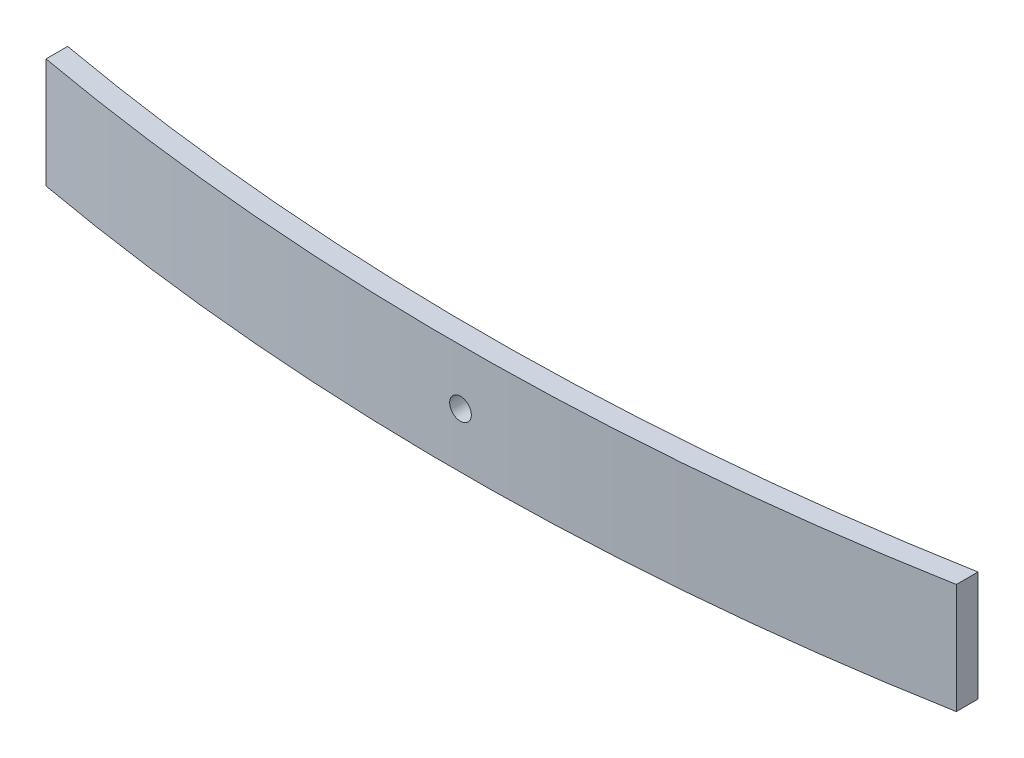
SolidWorks part; units mm, degrees
ref_plane "Front Plane" through (0, 0, 0) normal (0, 0, 1) x (1, 0, 0)
ref_plane "Top Plane" through (0, 0, 0) normal (0, 1, 0) x (1, 0, 0)
ref_plane "Right Plane" through (0, 0, 0) normal (1, 0, 0) x (0, 0, -1)
sketch "Sketch1" plane through (0, 0, 0) normal (0, 1, 0) x (1, 0, 0)
  line L0 (-630, 0) -> (630, 0) construction
  line L1 (-210.8013, -133) -> (245.5549, -133) construction
  line L2 (0, 0) -> (0, -133) construction
  line L3 (-602.5798, 17.4465) -> (-589.9243, 25.4988)
  line L4 (-616.835, -11.5296) -> (-605.5506, -21.4121)
  line L5 (616.835, -11.5296) -> (605.5506, -21.4121)
  line L6 (-630.0217, -47.5) -> (-630.0217, -62.5)
  line L7 (602.5798, 17.4465) -> (589.9243, 25.4988)
  line L8 (630.0217, -47.5) -> (630.0217, -62.5)
  line L9 (-545.0217, -92.3065) -> (-545.0217, -107.3065)
  line L10 (545.0217, -92.3065) -> (545.0217, -107.3065)
  line L11 (-485.0217, -125.4896) -> (-485.0217, -140.4896)
  line L12 (485.0217, -125.4896) -> (485.0217, -140.4896)
  line L13 (-425.0217, -156.3949) -> (-425.0217, -171.3949)
  line L14 (425.0217, -156.3949) -> (425.0217, -171.3949)
  line L15 (-315.0217, -194.8387) -> (-315.0217, -209.8387)
  line L16 (315.0217, -194.8387) -> (315.0217, -209.8387)
  arc A0 (-616.835, -11.5296) -> (-630, -17.5) centre (-630, 0) ccw
  arc A1 (630, -17.5) -> (616.835, -11.5296) centre (630, 0) ccw
  arc A2 (-630, -17.5) -> (630, -17.5) centre (0, 1642.9318) ccw
  arc A3 (-630.0011, -32.5) -> (630.0011, -32.5) centre (0, 1627.9379) ccw
  arc A4 (-605.5506, -21.4121) -> (-630.0011, -32.5) centre (-630, 0) ccw
  arc A5 (630.0011, -32.5) -> (605.5506, -21.4121) centre (630, 0) ccw
  arc A6 (-630.0217, -47.5) -> (630.0217, -47.5) centre (0, 1613.05) ccw
  arc A7 (630.0217, -47.5) -> (589.9243, 25.4988) centre (630, 0) ccw
  arc A8 (-589.9243, 25.4988) -> (-630.0217, -47.5) centre (-630, 0) ccw
  arc A9 (-630.0217, -62.5) -> (630.0217, -62.5) centre (0, 1598.05) ccw
  arc A10 (545.0217, -107.3065) -> (-545.0217, -107.3065) centre (0, 1583.05) cw
  arc A11 (485.0217, -140.4896) -> (-485.0217, -140.4896) centre (0, 1568.05) cw
  arc A12 (425.0217, -171.3949) -> (-425.0217, -171.3949) centre (0, 1553.05) cw
  arc A13 (315.0217, -209.8387) -> (-315.0217, -209.8387) centre (0, 1538.05) cw
  point P5 (-630.0217, -47.5)
  point P6 (0, -163)
  point P10 (0, -133)
  point P13 (-630.0011, -32.5)
  point P14 (0, -148)
  point P15 (630.0011, -32.5)
  point P20 (630.0217, -47.5)
  point P27 (0, -178)
  point P37 (0, -193)
  point P40 (630.0217, -55)
  point P44 (0, -208)
  point P50 (0, -223)
  point P56 (0, -238)
  dimension "D4" = 35
  dimension "D5" = 35
  dimension "D9" = 15
  dimension "D12" = 15
  dimension "D1" = 133
  dimension "D2" = 630
  dimension "D3" = 630
  dimension "D6" = 15
  dimension "D7" = 15
  dimension "D8" = 15
  dimension "D10" = 15
  dimension "D11" = 15
  dimension "D13" = 15
  dimension "D14" = 15
  dimension "D15" = 15
  dimension "D16" = 85
  dimension "D17" = 15
  dimension "D18" = 15
  dimension "D19" = 85
  dimension "D20" = 60
  dimension "D21" = 15
  dimension "D22" = 15
  dimension "D23" = 15
  dimension "D24" = 60
  dimension "D25" = 15
  dimension "D26" = 60
  dimension "D27" = 15
  dimension "D28" = 60
  dimension "D29" = 15
  dimension "D30" = 15
  dimension "D31" = 110
  dimension "D32" = 15
  dimension "D33" = 110
  dimension "D34" = 15
sketch "Sketch5" plane through (0, 0, 0) normal (0, 0, 1) x (1, 0, 0)
  circle A0 centre (0, 38.1) radius 7.5
  dimension "D2" = 15
  dimension "D1" = 38.1
sketch "Sketch6" plane through (0, 0, 0) normal (0, 0, 1) x (1, 0, 0)
  circle A0 centre (0, 38.1) radius 7.5
sketch "Sketch7" plane through (0, 0, 0) normal (0, 0, 1) x (1, 0, 0)
  circle A0 centre (0, 38.1) radius 7.5
sketch "Sketch8" plane through (0, 0, 0) normal (0, 0, 1) x (1, 0, 0)
  circle A0 centre (0, 38.1) radius 7.5
sketch "Sketch9" plane through (0, 0, 0) normal (0, 0, 1) x (1, 0, 0)
  circle A0 centre (0, 38.1) radius 7.5
sketch "Sketch10" plane through (0, 0, 0) normal (0, 0, 1) x (1, 0, 0)
  circle A0 centre (0, 38.1) radius 7.5
extrude "Boss-Extrude1" add sketch "Sketch1" along normal blind 76.2 contours A13 L16 A12 L15
sketch "Sketch11" plane through (0, 0, 0) normal (0, 0, 1) x (1, 0, 0)
  circle A0 centre (0, 38.1) radius 7.5
extrude "Cut-Extrude1" cut sketch "Sketch11" along normal through all
